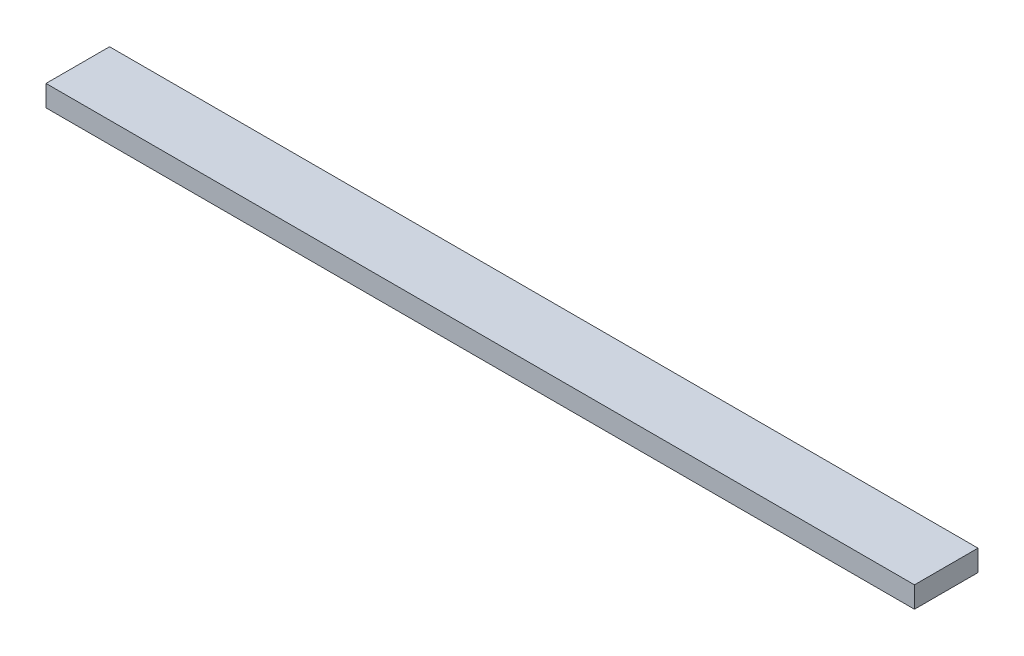
SolidWorks part; units mm, degrees
ref_plane "Front Plane" through (0, 0, 0) normal (0, 0, 1) x (1, 0, 0)
ref_plane "Top Plane" through (0, 0, 0) normal (0, 1, 0) x (1, 0, 0)
ref_plane "Right Plane" through (0, 0, 0) normal (1, 0, 0) x (0, 0, -1)
sketch "Sketch1" plane through (0, 0, 0) normal (0, 1, 0) x (1, 0, 0)
  line L0 (-205, 15) -> (205, -15) construction
  line L1 (-205, 15) -> (205, 15)
  line L2 (-205, 15) -> (-205, -15)
  line L3 (-205, -15) -> (205, -15)
  line L4 (205, 15) -> (205, -15)
  dimension "D1" = 410
  dimension "D2" = 30
extrude "Boss-Extrude1" add sketch "Sketch1" along normal blind 10
